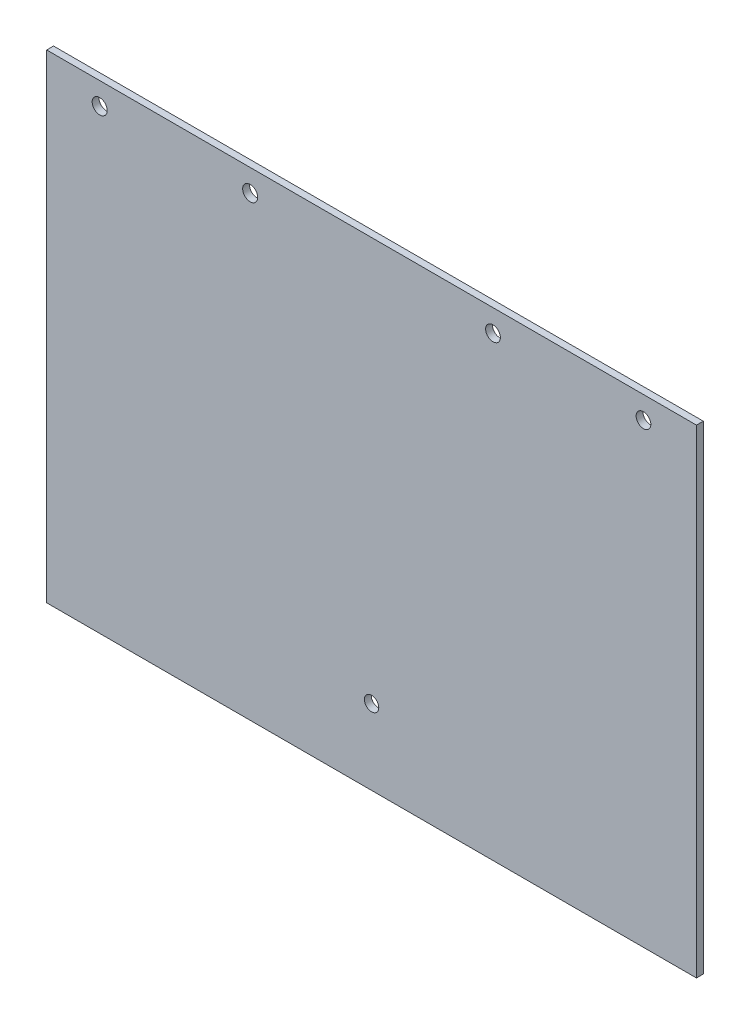
SolidWorks part; units mm, degrees
material "ｱｸﾘﾙ (中-上級の耐衝撃性)"
ref_plane "正面" through (0, 0, 0) normal (0, 0, 1) x (1, 0, 0)
ref_plane "平面" through (0, 0, 0) normal (0, 1, 0) x (1, 0, 0)
ref_plane "右側面" through (0, 0, 0) normal (1, 0, 0) x (0, 0, -1)
sketch "ｽｹｯﾁ1" plane through (0, 0, 0) normal (0, 0, 1) x (1, 0, 0)
  line L1 (-95, 70) -> (95, 70)
  line L2 (-95, 70) -> (-95, -70)
  line L3 (-95, -70) -> (95, -70)
  line L4 (95, 70) -> (95, -70)
  line L5 (-95, 70) -> (95, -70) construction
  line L6 (-95, -70) -> (95, 70) construction
  point P0 (0, 0)
  dimension "D1" = 190
  dimension "D2" = 140
extrude "ﾎﾞｽ - 押し出し1" add sketch "ｽｹｯﾁ1" along normal blind 2 contours L2 L1 L4 L3
sketch "ｽｹｯﾁ2" plane through (0, 0, 2) normal (0, 0, 1) x (1, 0, 0)
  line L0 (-95, 70) -> (-95, 63.5)
  line L1 (-95, 70) -> (-95, -70) construction
  line L2 (-95, 63.5) -> (0, 63.5)
  line L3 (0, 63.5) -> (35.5, 63.5)
  line L4 (0, 63.5) -> (79.5, 63.5)
  line L5 (0, 63.5) -> (-35.5, 63.5)
  line L6 (0, 63.5) -> (-79.5, 63.5)
  circle A0 centre (35.5, 63.5) radius 2.15
  circle A1 centre (79.5, 63.5) radius 2.15
  circle A2 centre (-35.5, 63.5) radius 2.2
  circle A3 centre (-79.5, 63.5) radius 2.2
  dimension "D5" = 4.3
  dimension "D6" = 4.3
  dimension "D9" = 4.4
  dimension "D10" = 4.4
  dimension "D1" = 6.5
  dimension "D2" = 95
  dimension "D3" = 35.5
  dimension "D4" = 79.5
  dimension "D7" = 35.5
  dimension "D8" = 79.5
extrude "ｶｯﾄ - 押し出し1" cut sketch "ｽｹｯﾁ2" against normal blind 10
sketch "ｽｹｯﾁ3" plane through (0, 0, 2) normal (0, 0, 1) x (1, 0, 0)
  line L0 (-95, -70) -> (0, -70)
  line L1 (-95, -70) -> (95, -70) construction
  line L2 (0, -70) -> (0, -48)
  circle A0 centre (0, -48) radius 2.1
  dimension "D2" = 4.2
  dimension "D1" = 22
extrude "ｶｯﾄ - 押し出し2" cut sketch "ｽｹｯﾁ3" against normal blind 10
